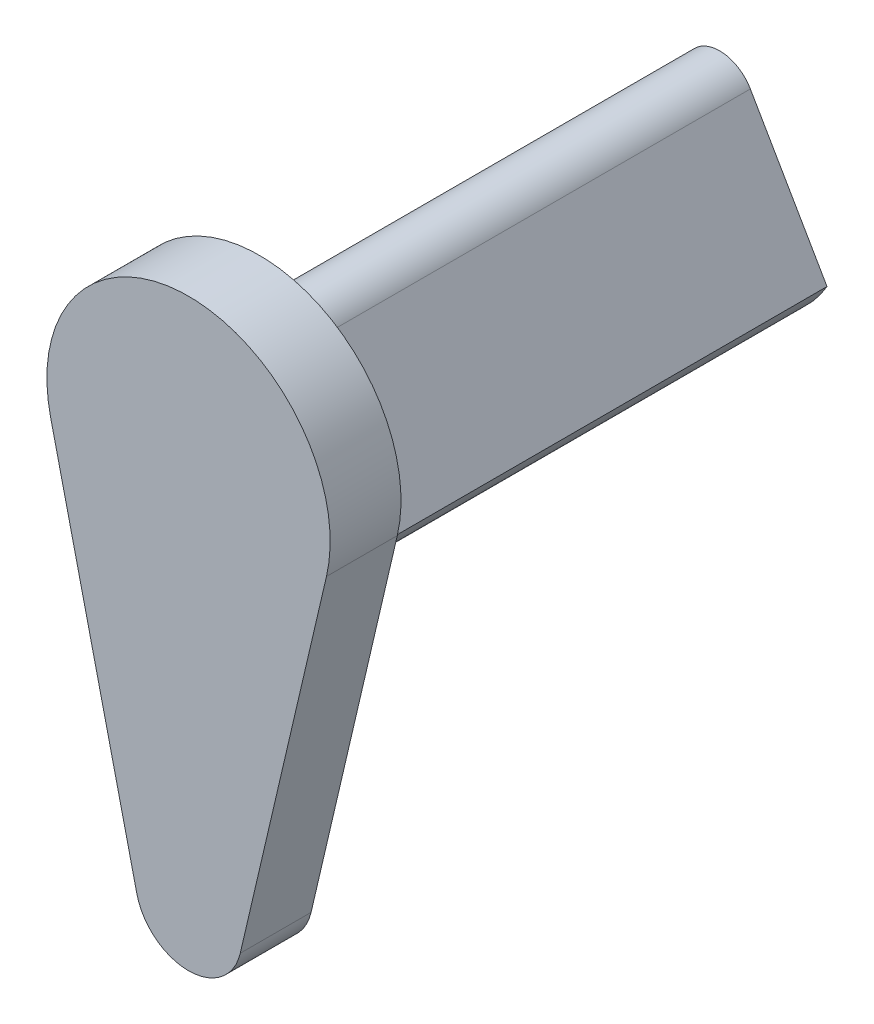
SolidWorks part; units mm, degrees
ref_plane "前视基准面" through (0, 0, 0) normal (0, 0, 1) x (1, 0, 0)
ref_plane "上视基准面" through (0, 0, 0) normal (0, 1, 0) x (1, 0, 0)
ref_plane "右视基准面" through (0, 0, 0) normal (1, 0, 0) x (0, 0, -1)
sketch "草图1" plane through (0, 0, 0) normal (0, 0, 1) x (1, 0, 0)
  circle A0 centre (0, 0) radius 3.5
  dimension "D1" = 7
extrude "凸台-拉伸1" add sketch "草图1" along normal blind 13
sketch "草图2" plane through (0, 0, 13) normal (0, 0, 1) x (1, 0, 0)
  line L0 (0, -11) -> (0, 0) construction
  line L1 (-3.8953, -0.9091) -> (-1.4607, -11.3409)
  line L2 (3.8953, -0.9091) -> (1.4607, -11.3409)
  arc A0 (3.8953, -0.9091) -> (-3.8953, -0.9091) centre (0, 0) ccw
  arc A1 (-1.4607, -11.3409) -> (1.4607, -11.3409) centre (0, -11) ccw
  dimension "D1" = 8
  dimension "D2" = 3
  dimension "D3" = 11
extrude "凸台-拉伸2" add sketch "草图2" along normal blind 2
sketch "草图3" plane through (0, 0, 0) normal (0, 0, -1) x (-1, 0, 0)
  line L0 (0, 0) -> (0, 3.5) construction
  line L1 (0, 3.5) -> (-3.0311, -1.75)
  line L2 (-3.0311, -1.75) -> (-6.7599, -1.75)
  line L3 (-6.7599, -1.75) -> (0, 7.7423)
  line L4 (6.7599, -1.75) -> (0, 7.7423)
  line L5 (3.0311, -1.75) -> (6.7599, -1.75)
  line L6 (0, 3.5) -> (3.0311, -1.75)
  circle A0 centre (0, 0) radius 3.5 construction
  dimension "D1" = 60
extrude "切除-拉伸1" cut sketch "草图3" against normal up to surface (13 mm away) up to face at (3.5, 0, 13)
sketch "草图4" plane through (0, 0, 0) normal (0, 0, -1) x (-1, 0, 0)
  circle A0 centre (0, 0) radius 1.25
  dimension "D1" = 2.5
extrude "切除-拉伸2" cut sketch "草图4" against normal blind 8
cosmetic thread "装饰螺纹线1" parameters "D2"=3
fillet "圆角1" radius 1 1 edges at (0, 3.5, 6.5)
equation "\"2。5\"=3"
